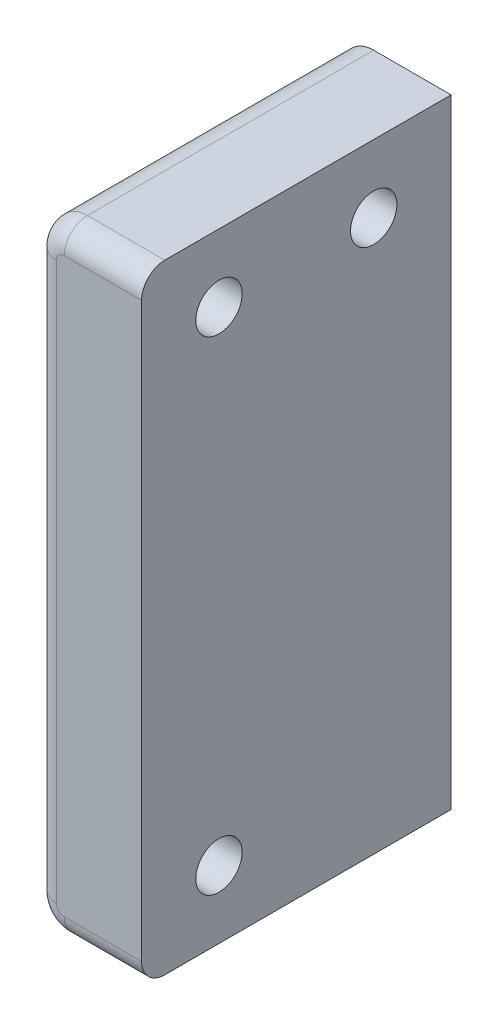
SolidWorks part; units mm, degrees
ref_plane "Front Plane" through (0, 0, 0) normal (0, 0, 1) x (1, 0, 0)
ref_plane "Top Plane" through (0, 0, 0) normal (0, 1, 0) x (1, 0, 0)
ref_plane "Right Plane" through (0, 0, 0) normal (1, 0, 0) x (0, 0, -1)
sketch "Sketch2" plane through (0, 0, 0) normal (0, 0, 1) x (1, 0, 0)
  line L0 (-148, -68) -> (-132, -68) construction
  line L1 (-148, -28) -> (-153, -28)
  line L2 (-148, -28) -> (-148, -68)
  line L3 (-148, -68) -> (-153, -68)
  line L4 (-155, -30) -> (-155, -66)
  arc A0 (-153, -68) -> (-155, -66) centre (-153, -66) cw
  arc A1 (-153, -28) -> (-155, -30) centre (-153, -30) ccw
  point P10 (-155, -68)
extrude "Boss-Extrude1" add sketch "Sketch2" along normal up to surface (20 mm away)
sketch "Sketch3" plane through (-148, 0, 0) normal (1, 0, 0) x (0, 0, -1)
  circle A0 centre (-15, -63.625) radius 1.5
  circle A2 centre (-5, -32.375) radius 1.5
  circle A3 centre (-15, -32.375) radius 1.5
extrude "Cut-Extrude1" cut sketch "Sketch3" against normal blind 10
fillet "Fillet1" radius 1.5 5 edges at (-150.5, -68, 20) (-154.4142, -67.4142, 20) (-155, -48, 20) (-154.4142, -28.5858, 20) (-150.5, -28, 20)
